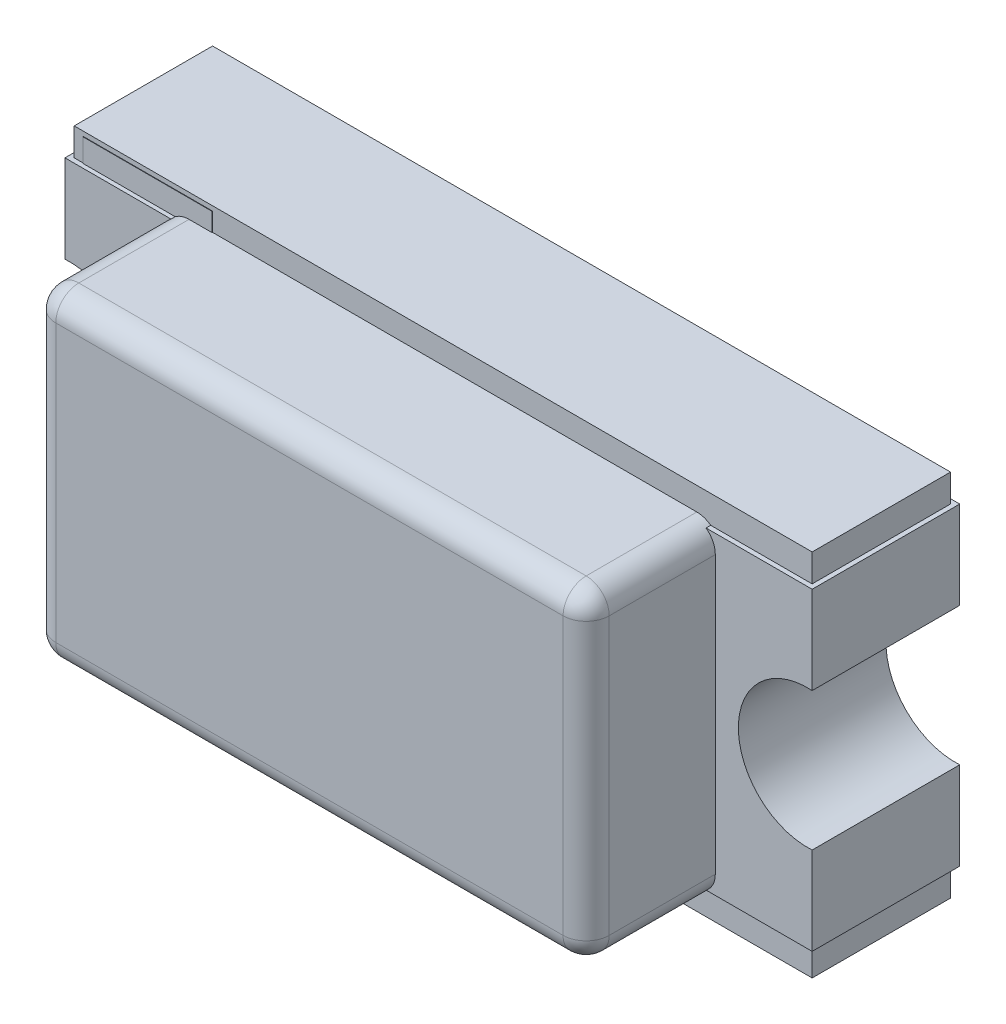
SolidWorks part; units mm, degrees
ref_plane "Спереди" through (0, 0, 0) normal (0, 0, 1) x (1, 0, 0)
ref_plane "Сверху" through (0, 0, 0) normal (0, 1, 0) x (1, 0, 0)
ref_plane "Справа" through (0, 0, 0) normal (1, 0, 0) x (0, 0, -1)
sketch "Эскиз2" plane through (0, 0, 0) normal (0, 0, 1) x (1, 0, 0)
  line L1 (-0.8, 0.4) -> (0.8, 0.4)
  line L2 (-0.8, 0.4) -> (-0.8, -0.4)
  line L3 (-0.8, -0.4) -> (0.8, -0.4)
  line L4 (0.8, 0.4) -> (0.8, -0.4)
  point P0 (0, 0)
extrude "Бобышка-Вытянуть1" add sketch "Эскиз2" along normal blind 0.3 from offset 0.01
sketch "Эскиз3" plane through (0, 0, 0) normal (0, 0, 1) x (1, 0, 0)
  line L1 (-0.81, 0.34) -> (-0.5, 0.34)
  line L2 (-0.81, 0.34) -> (-0.81, -0.34)
  line L3 (-0.81, -0.34) -> (-0.5, -0.34)
  line L4 (-0.5, 0.34) -> (-0.5, -0.34)
  line L5 (0.5, 0.34) -> (0.81, 0.34)
  line L6 (0.5, 0.34) -> (0.5, -0.34)
  line L7 (0.5, -0.34) -> (0.81, -0.34)
  line L8 (0.81, 0.34) -> (0.81, -0.34)
extrude "Бобышка-Вытянуть2" add sketch "Эскиз3" along normal blind 0.32
sketch "Эскиз4" plane through (0, 0, 0) normal (0, 0, 1) x (1, 0, 0)
  line L1 (-0.6, 0.35) -> (0.6, 0.35)
  line L2 (-0.6, 0.35) -> (-0.6, -0.35)
  line L3 (-0.6, -0.35) -> (0.6, -0.35)
  line L4 (0.6, 0.35) -> (0.6, -0.35)
extrude "Бобышка-Вытянуть3" add sketch "Эскиз4" along normal blind 0.3 from offset 0.3
fillet "Скругление1" radius 0.05 8 edges at (0.6, 0.35, 0.455) (-0.6, 0.35, 0.455) (0, 0.35, 0.6) (0.6, 0, 0.6) (0.6, -0.35, 0.455) (-0.6, -0.35, 0.455) (0, -0.35, 0.6) (-0.6, 0, 0.6)
sketch "Эскиз5" plane through (0, 0, 0.31) normal (0, 0, 1) x (1, 0, 0)
  line L1 (-0.78, 0.39) -> (-0.5, 0.39)
  line L2 (-0.78, 0.39) -> (-0.78, -0.39)
  line L3 (-0.78, -0.39) -> (-0.5, -0.39)
  line L4 (-0.5, 0.39) -> (-0.5, -0.39)
extrude "Бобышка-Вытянуть4" add sketch "Эскиз5" along normal blind 0.001
sketch "Эскиз6" plane through (0, 0, 0) normal (0, 0, 1) x (1, 0, 0)
  circle A0 centre (-0.8, 0) radius 0.15
  circle A1 centre (0.8, 0) radius 0.15
extrude "Вырез-Вытянуть2" cut sketch "Эскиз6" along normal blind 0.52
